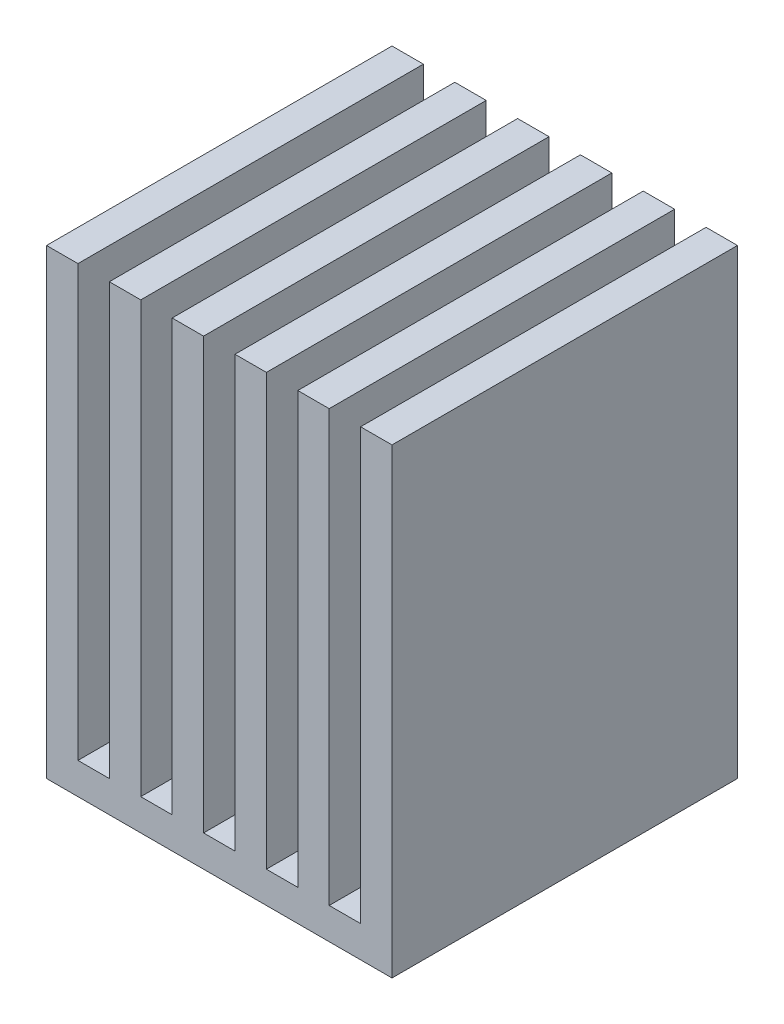
SolidWorks part; units mm, degrees
ref_plane "Front Plane" through (0, 0, 0) normal (0, 0, 1) x (1, 0, 0)
ref_plane "Top Plane" through (0, 0, 0) normal (0, 1, 0) x (1, 0, 0)
ref_plane "Right Plane" through (0, 0, 0) normal (1, 0, 0) x (0, 0, -1)
sketch "Sketch3" plane through (0, 0, 0) normal (0, 1, 0) x (1, 0, 0)
  line L1 (-20, -20) -> (20, -20)
  line L2 (-20, -20) -> (-20, 20)
  line L3 (-20, 20) -> (20, 20)
  line L4 (20, -20) -> (20, 20)
  line L5 (-20, -20) -> (20, 20) construction
  line L6 (-20, 20) -> (20, -20) construction
  point P0 (0, 0)
  dimension "D1" = 40
extrude "Boss-Extrude2" add sketch "Sketch3" along normal mid plane 10
sketch "Sketch5" plane through (0, 0, 0) normal (1, 0, 0) x (0, 0, -1)
  line L0 (-20, -5) -> (20, -5) construction
  line L1 (-62.5, 152) -> (62.5, 152)
  line L2 (-62.5, 152) -> (-62.5, 30)
  line L3 (-62.5, 30) -> (62.5, 30)
  line L4 (62.5, 152) -> (62.5, 30)
  line L5 (-62.5, 152) -> (62.5, 30) construction
  line L6 (-62.5, 30) -> (62.5, 152) construction
  point P0 (0, 91)
  dimension "D1" = 122
  dimension "D2" = 125
  dimension "D3" = 157
  dimension "D4" = 35
sketch "Sketch8" plane through (0, 5, 0) normal (0, 1, 0) x (1, 0, 0)
  line L1 (-62.5, -55) -> (62.5, -55)
  line L2 (-62.5, -55) -> (-62.5, 55)
  line L3 (-62.5, 55) -> (62.5, 55)
  line L4 (62.5, -55) -> (62.5, 55)
  line L5 (-62.5, -55) -> (62.5, 55) construction
  line L6 (-62.5, 55) -> (62.5, -55) construction
  point P0 (0, 0)
  dimension "D1" = 110
  dimension "D2" = 125
sketch "Sketch9" plane through (0, 0, 0) normal (0, 0, 1) x (1, 0, 0)
  line L0 (-55, 5) -> (55, 5)
  line L2 (-62.5, 5) -> (62.5, 5) construction
  line L4 (55, 5) -> (55, 152)
  line L5 (55, 152) -> (45, 152)
  line L6 (45, 152) -> (45, 15)
  line L7 (45, 15) -> (35, 15)
  line L8 (55, 15) -> (-55, 15)
  line L9 (35, 152) -> (35, 15)
  line L10 (35, 152) -> (25, 152)
  line L11 (15, 152) -> (5, 152)
  line L12 (-5, 152) -> (-15, 152)
  line L13 (-25, 152) -> (-35, 152)
  line L14 (-45, 152) -> (-55, 152)
  line L15 (25, 152) -> (25, 15)
  line L16 (15, 152) -> (15, 15)
  line L17 (5, 152) -> (5, 15)
  line L18 (-5, 152) -> (-5, 15)
  line L19 (-15, 152) -> (-15, 15)
  line L20 (-25, 152) -> (-25, 15)
  line L21 (-35, 152) -> (-35, 15)
  line L22 (-45, 152) -> (-45, 15)
  line L23 (-55, 152) -> (-55, 5)
  line L24 (25, 15) -> (15, 15)
  line L25 (5, 15) -> (-5, 15)
  line L26 (-15, 15) -> (-25, 15)
  line L27 (-35, 15) -> (-45, 15)
  dimension "D2" = 10
  dimension "D6" = 147
  dimension "D7" = 10
  dimension "D1" = 6
  dimension "D3" = 11
  dimension "D4" = 5
extrude "Boss-Extrude3" add sketch "Sketch9" along normal mid plane 110 contours L14 L23 L8 L22 | L13 L21 L8 L20 | L12 L19 L8 L18 | L11 L17 L8 L16 | L10 L15 L8 L9 | L8 L4 L5 L6 | L8 L23 L0 L4 L7 L26
